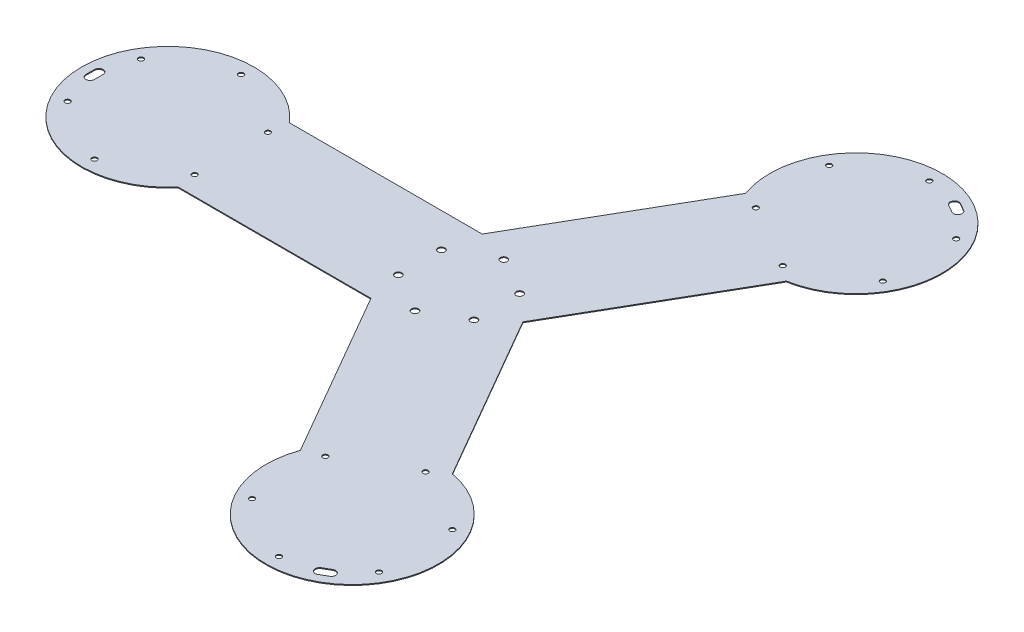
SolidWorks part; units mm, degrees
material "1060 Alloy"
ref_plane "Front Plane" through (0, 0, 0) normal (0, 0, 1) x (1, 0, 0)
ref_plane "Top Plane" through (0, 0, 0) normal (0, 1, 0) x (1, 0, 0)
ref_plane "Right Plane" through (0, 0, 0) normal (1, 0, 0) x (0, 0, -1)
sketch "Sketch1" plane through (0, 0, 0) normal (0, 1, 0) x (1, 0, 0)
  line L0 (-37.2391, -64.5) -> (-260.8208, -64.5)
  line L1 (74.5518, 258.1275) -> (-37.2391, 64.5)
  line L2 (-422.2391, -5) -> (-422.2391, 5) construction
  line L3 (-427.2391, -5) -> (-427.2391, 5)
  line L5 (-260.8208, 64.5) -> (-37.2391, 64.5)
  line L6 (186.2691, 193.6275) -> (74.4782, 0)
  line L8 (74.4782, 0) -> (186.2691, -193.6275)
  line L9 (-37.2391, -64.5) -> (74.5518, -258.1275)
  line L10 (-417.2391, -5) -> (-417.2391, 5)
  line L11 (206.7894, 368.1698) -> (215.4497, 363.1698) construction
  line L12 (209.2894, 372.4999) -> (217.9497, 367.4999)
  line L13 (204.2894, 363.8397) -> (212.9497, 358.8397)
  line L14 (215.4497, -363.1698) -> (206.7894, -368.1698) construction
  line L15 (217.9497, -367.4999) -> (209.2894, -372.4999)
  line L16 (212.9497, -358.8397) -> (204.2894, -363.8397)
  line L17 (74.4782, 0) -> (-37.2391, -64.5) construction
  line L18 (74.4782, 0) -> (-37.2391, 64.5) construction
  line L19 (0.8494, 51.4711) -> (44.1506, 26.4711) construction
  line L20 (22.5, 38.9711) -> (0, 0) construction
  arc A0 (-260.8208, 64.5) -> (-260.8208, -64.5) centre (-337.2391, 0) ccw
  arc A1 (74.5518, -258.1275) -> (186.2691, -193.6275) centre (168.6195, -292.0576) ccw
  arc A2 (74.5518, 258.1275) -> (186.2691, 193.6275) centre (168.6195, 292.0576) cw
  circle A3 centre (-337.2391, 85) radius 3
  circle A4 centre (-263.6269, 42.5) radius 3
  circle A5 centre (-263.6269, -42.5) radius 3
  circle A6 centre (-337.2391, -85) radius 3
  circle A7 centre (-410.8513, -42.5) radius 3
  circle A8 centre (-410.8513, 42.5) radius 3
  arc A9 (-427.2391, -5) -> (-417.2391, -5) centre (-422.2391, -5) ccw
  arc A10 (-417.2391, 5) -> (-427.2391, 5) centre (-422.2391, 5) ccw
  circle A11 centre (168.6195, 207.0576) radius 3
  circle A12 centre (242.2317, 249.5576) radius 3
  circle A13 centre (242.2317, 334.5576) radius 3
  circle A14 centre (168.6195, 377.0576) radius 3
  circle A15 centre (95.0074, 334.5576) radius 3
  circle A16 centre (95.0074, 249.5576) radius 3
  arc A17 (209.2894, 372.4999) -> (204.2894, 363.8397) centre (206.7894, 368.1698) ccw
  arc A18 (212.9497, 358.8397) -> (217.9497, 367.4999) centre (215.4497, 363.1698) ccw
  circle A19 centre (95.0074, -249.5576) radius 3
  circle A20 centre (95.0074, -334.5576) radius 3
  circle A21 centre (168.6195, -377.0576) radius 3
  circle A22 centre (242.2317, -334.5576) radius 3
  circle A23 centre (242.2317, -249.5576) radius 3
  circle A24 centre (168.6195, -207.0576) radius 3
  arc A25 (217.9497, -367.4999) -> (212.9497, -358.8397) centre (215.4497, -363.1698) ccw
  arc A26 (204.2894, -363.8397) -> (209.2894, -372.4999) centre (206.7894, -368.1698) ccw
  circle A30 centre (-45, -25) radius 4
  circle A31 centre (-45, 25) radius 4
  circle A32 centre (44.1506, 26.4711) radius 4
  circle A33 centre (0.8494, 51.4711) radius 4
  circle A34 centre (0.8494, -51.4711) radius 4
  circle A35 centre (44.1506, -26.4711) radius 4
  point P27 (-337.2391, 0)
  point P28 (-422.2391, 0)
  point P49 (211.1195, 365.6698)
  point P68 (211.1195, -365.6698)
  point P73 (0, 0)
  point P80 (0, 0)
  point P87 (0, 0)
  dimension "D5" = 100
  dimension "D12" = 100
  dimension "D19" = 100
  dimension "D20" = 6
  dimension "D33" = 8
  dimension "D34" = 8
  dimension "D13" = 0
  dimension "D14" = 0
  dimension "D3" = 64.5
  dimension "D9" = 64.5
  dimension "D4" = 64.5
  dimension "D7" = 120
  dimension "D8" = 64.5
  dimension "D10" = 64.5
  dimension "D11" = 120
  dimension "D18" = 64.5
  dimension "D21" = 0
  dimension "D22" = 85
  dimension "D24" = 85
  dimension "D25" = 42.5
  dimension "D26" = 10
  dimension "D27" = 10
  dimension "D28" = 0
  dimension "D29" = 85
  dimension "D16" = 300
  dimension "D15" = 300
  dimension "D17" = 223.5817
  dimension "D31" = 300
  dimension "D6" = 0
  dimension "D32" = 223.5817
  dimension "D35" = 25
  dimension "D36" = 25
  dimension "D37" = 45
  dimension "D38" = 45
  dimension "D40" = 39.5
  dimension "D41" = 45
  dimension "D23" = 6
  dimension "D30" = 3
  dimension "D39" = 3
extrude "Boss-Extrude1" add sketch "Sketch1" along normal blind 1
equation "\"rad\"=64.5"
equation "\"D3@Sketch1\"=\"rad\""
equation "\"D9@Sketch1\"=\"rad\""
equation "\"D8@Sketch1\"=\"rad\""
equation "\"D10@Sketch1\"=\"rad\""
equation "\"D18@Sketch1\"=\"rad\""
equation "\"D4@Sketch1\"=\"rad\""
